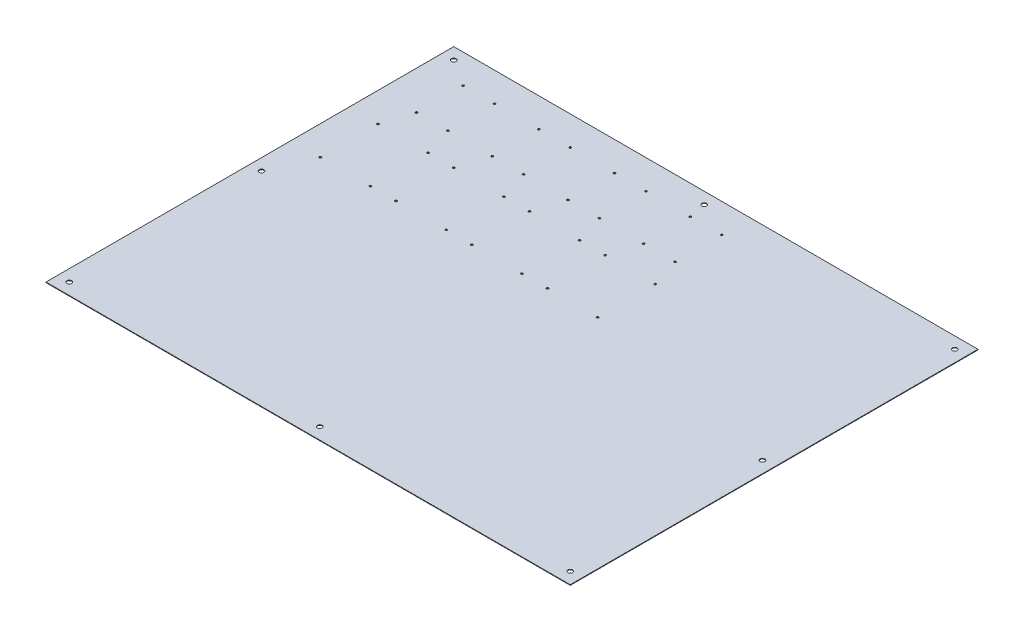
SolidWorks part; units mm, degrees
ref_plane "Front Plane" through (0, 0, 0) normal (0, 0, 1) x (1, 0, 0)
ref_plane "Top Plane" through (0, 0, 0) normal (0, 1, 0) x (1, 0, 0)
ref_plane "Right Plane" through (0, 0, 0) normal (1, 0, 0) x (0, 0, -1)
sketch "Sketch1" plane through (0, 0, 0) normal (0, 1, 0) x (1, 0, 0)
  line L0 (0, 90) -> (0, 0) construction
  line L1 (-27, 130) -> (27, 130) construction
  line L2 (-27, 130) -> (-27, 50) construction
  line L3 (-27, 50) -> (27, 50) construction
  line L4 (27, 130) -> (27, 50) construction
  line L5 (-27, 130) -> (27, 50) construction
  line L6 (-27, 50) -> (27, 130) construction
  line L7 (130, 90) -> (130, 0) construction
  line L8 (-43, 0) -> (43, 0) construction
  line L9 (-43, 0) -> (-43, -99) construction
  line L10 (-43, -99) -> (43, -99) construction
  line L11 (43, 0) -> (43, -99) construction
  line L12 (-43, 0) -> (43, -99) construction
  line L13 (-43, -99) -> (43, 0) construction
  line L14 (103, 130) -> (157, 130) construction
  line L15 (103, 130) -> (103, 50) construction
  line L16 (103, 50) -> (157, 50) construction
  line L17 (157, 130) -> (157, 50) construction
  line L18 (103, 130) -> (157, 50) construction
  line L19 (103, 50) -> (157, 130) construction
  line L20 (87, 0) -> (173, 0) construction
  line L21 (87, 0) -> (87, -99) construction
  line L22 (87, -99) -> (173, -99) construction
  line L23 (173, 0) -> (173, -99) construction
  line L24 (87, 0) -> (173, -99) construction
  line L25 (87, -99) -> (173, 0) construction
  line L26 (260, 90) -> (260, 0) construction
  line L27 (233, 130) -> (287, 130) construction
  line L28 (233, 130) -> (233, 50) construction
  line L29 (233, 50) -> (287, 50) construction
  line L30 (287, 130) -> (287, 50) construction
  line L31 (233, 130) -> (287, 50) construction
  line L32 (233, 50) -> (287, 130) construction
  line L33 (217, 0) -> (303, 0) construction
  line L34 (217, 0) -> (217, -99) construction
  line L35 (217, -99) -> (303, -99) construction
  line L36 (303, 0) -> (303, -99) construction
  line L37 (217, 0) -> (303, -99) construction
  line L38 (217, -99) -> (303, 0) construction
  line L39 (390, 90) -> (390, 0) construction
  line L40 (363, 130) -> (417, 130) construction
  line L41 (363, 130) -> (363, 50) construction
  line L42 (363, 50) -> (417, 50) construction
  line L43 (417, 130) -> (417, 50) construction
  line L44 (363, 130) -> (417, 50) construction
  line L45 (363, 50) -> (417, 130) construction
  line L46 (347, 0) -> (433, 0) construction
  line L47 (347, 0) -> (347, -99) construction
  line L48 (347, -99) -> (433, -99) construction
  line L49 (433, 0) -> (433, -99) construction
  line L50 (347, 0) -> (433, -99) construction
  line L51 (347, -99) -> (433, 0) construction
  line L52 (-73, -170) -> (787, -170) construction
  line L53 (-93, 180) -> (807, 180)
  line L54 (-93, 180) -> (-93, -520)
  line L55 (-93, -520) -> (807, -520)
  line L56 (807, 180) -> (807, -520)
  line L57 (-73, 160) -> (787, 160) construction
  line L58 (-73, 160) -> (-73, -500) construction
  line L59 (-73, -500) -> (787, -500) construction
  line L60 (787, 160) -> (787, -500) construction
  circle A0 centre (-27, 130) radius 1.75
  circle A1 centre (27, 130) radius 1.75
  circle A2 centre (27, 50) radius 1.75
  circle A3 centre (-27, 50) radius 1.75
  circle A4 centre (-43, 0) radius 1.75
  circle A5 centre (43, 0) radius 1.75
  circle A6 centre (43, -99) radius 1.75
  circle A7 centre (-43, -99) radius 1.75
  circle A8 centre (103, 130) radius 1.75
  circle A9 centre (157, 130) radius 1.75
  circle A10 centre (157, 50) radius 1.75
  circle A11 centre (103, 50) radius 1.75
  circle A12 centre (87, 0) radius 1.75
  circle A13 centre (173, 0) radius 1.75
  circle A14 centre (173, -99) radius 1.75
  circle A15 centre (87, -99) radius 1.75
  circle A16 centre (233, 130) radius 1.75
  circle A17 centre (287, 130) radius 1.75
  circle A18 centre (287, 50) radius 1.75
  circle A19 centre (233, 50) radius 1.75
  circle A20 centre (217, 0) radius 1.75
  circle A21 centre (303, 0) radius 1.75
  circle A22 centre (303, -99) radius 1.75
  circle A23 centre (217, -99) radius 1.75
  circle A24 centre (363, 130) radius 1.75
  circle A25 centre (417, 130) radius 1.75
  circle A26 centre (417, 50) radius 1.75
  circle A27 centre (363, 50) radius 1.75
  circle A28 centre (347, 0) radius 1.75
  circle A29 centre (433, 0) radius 1.75
  circle A30 centre (433, -99) radius 1.75
  circle A31 centre (347, -99) radius 1.75
  circle A32 centre (-73, 160) radius 4.1
  circle A33 centre (787, 160) radius 4.1
  circle A34 centre (787, -500) radius 4.1
  circle A35 centre (-73, -500) radius 4.1
  circle A36 centre (-73, -170) radius 4.1
  circle A37 centre (357, 160) radius 4.1
  circle A38 centre (787, -170) radius 4.1
  circle A39 centre (357, -500) radius 4.1
  point P0 (0, 90)
  point P8 (0, -49.5)
  point P22 (130, 90)
  point P29 (130, -49.5)
  point P42 (260, 90)
  point P49 (260, -49.5)
  point P62 (390, 90)
  point P69 (390, -49.5)
  dimension "D6" = 3.5
  dimension "D15" = 8.2
  dimension "D1" = 54
  dimension "D2" = 80
  dimension "D3" = 50
  dimension "D4" = 99
  dimension "D5" = 86
  dimension "D8" = 700
  dimension "D9" = 50
  dimension "D10" = 50
  dimension "D11" = 900
  dimension "D12" = 130
  dimension "D16" = 20
  dimension "D17" = 20
  dimension "D18" = 20
  dimension "D19" = 20
  dimension "D7" = 4
extrude "Boss-Extrude1" add sketch "Sketch1" along normal blind 1
